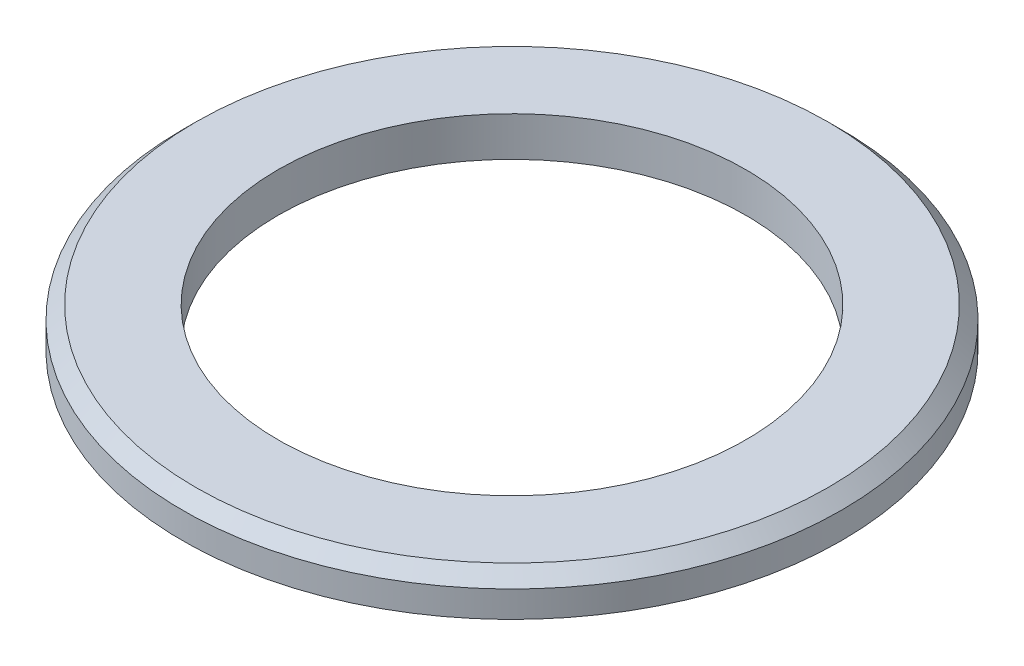
SolidWorks part; units mm, degrees
ref_plane "Front Plane" through (0, 0, 0) normal (0, 0, 1) x (1, 0, 0)
ref_plane "Top Plane" through (0, 0, 0) normal (0, 1, 0) x (1, 0, 0)
ref_plane "Right Plane" through (0, 0, 0) normal (1, 0, 0) x (0, 0, -1)
sketch "Sketch1" plane through (0, 0, 0) normal (0, 0, 1) x (1, 0, 0)
  line L0 (0, 0) -> (0, 3)
  line L1 (0, -100.0454) -> (0, 100.0454) construction
  line L2 (0, 3) -> (25, 3)
  line L3 (25, 3) -> (25, 0)
  line L5 (495.4813, 0) -> (-495.4813, 0) construction
  line L6 (0, 0) -> (25, 0)
  dimension "D1" = 25
  dimension "D2" = 3
revolve "Revolve1" add sketch "Sketch1" angle 360 about L3
sketch "Sketch2" plane through (0, 3, 0) normal (0, 1, 0) x (1, 0, 0)
  line L0 (25, 26.2029) -> (25, -28.1547) construction
  line L1 (-3.6874, 0) -> (53.6874, 0) construction
  line L2 (-1.65, 0) -> (1.65, 0) construction
  circle A0 centre (25, 0) radius 17.75
  circle A1 centre (25, 0) radius 25 construction
  dimension "D1" = 35.5
extrude "Cut-Extrude1" cut sketch "Sketch2" against normal blind 3
chamfer "Chamfer1" distance 1 angle 45 1 edges at (0, 3, 0)
